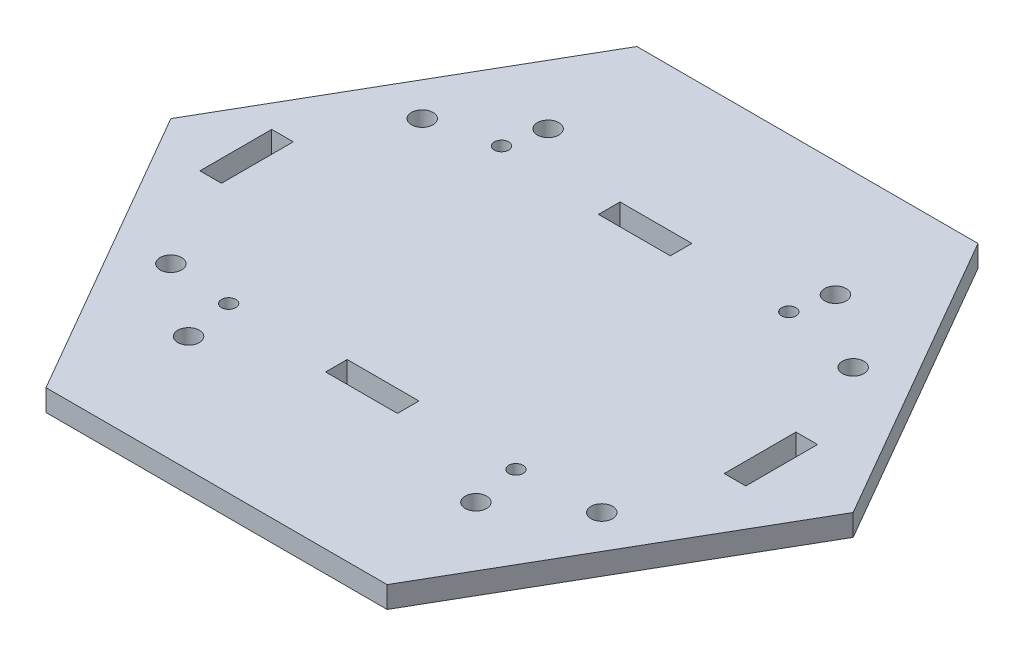
SolidWorks part; units mm, degrees
ref_plane "Alzado" through (0, 0, 0) normal (0, 0, 1) x (1, 0, 0)
ref_plane "Planta" through (0, 0, 0) normal (0, 1, 0) x (1, 0, 0)
ref_plane "Vista lateral" through (0, 0, 0) normal (1, 0, 0) x (0, 0, -1)
sketch "Croquis1" plane through (0, 0, 0) normal (0, 1, 0) x (1, 0, 0)
  line L1 (-47.5, 0) -> (-23.75, -41.1362)
  line L2 (-23.75, -41.1362) -> (23.75, -41.1362)
  line L3 (23.75, -41.1362) -> (47.5, 0)
  line L4 (47.5, 0) -> (23.75, 41.1362)
  line L5 (23.75, 41.1362) -> (-23.75, 41.1362)
  line L6 (-23.75, 41.1362) -> (-47.5, 0)
  circle A0 centre (0, 0) radius 41.1362 construction
  dimension "D1" = 95
extrude "Saliente-Extruir1" add sketch "Croquis1" along normal blind 3
sketch "Croquis3" plane through (0, 3, 0) normal (0, 1, 0) x (1, 0, 0)
  line L0 (-6.1776, 18.2235) -> (-6.1776, 21.2235)
  line L1 (33.8224, 5.7235) -> (33.8224, -4.2765)
  line L2 (3.8224, -16.7765) -> (-6.1776, -16.7765)
  line L3 (-36.1776, 5.7235) -> (-36.1776, -4.2765)
  line L4 (-6.1776, 21.2235) -> (3.8224, 21.2235)
  line L5 (3.8224, 21.2235) -> (3.8224, 18.2235)
  line L6 (33.8224, 5.7235) -> (36.8224, 5.7235)
  line L7 (36.8224, 5.7235) -> (36.8224, -4.2765)
  line L8 (36.8224, -4.2765) -> (33.8224, -4.2765)
  line L9 (-6.1776, -16.7765) -> (-6.1776, -19.7765)
  line L10 (-6.1776, -19.7765) -> (3.8224, -19.7765)
  line L11 (3.8224, -19.7765) -> (3.8224, -16.7765)
  line L12 (-36.1776, 5.7235) -> (-39.1776, 5.7235)
  line L13 (-39.1776, 5.7235) -> (-39.1776, -4.2765)
  line L14 (-39.1776, -4.2765) -> (-36.1776, -4.2765)
  line L15 (3.8224, 18.2235) -> (-6.1776, 18.2235)
  circle A0 centre (-21.1776, 19.7235) radius 1
  circle A1 centre (18.8224, 19.7235) radius 1
  circle A2 centre (18.8224, -18.2765) radius 1
  circle A3 centre (-21.1776, -18.2765) radius 1
extrude "Cortar-Extruir1" cut sketch "Croquis3" against normal through all
sketch "Croquis4" plane through (0, 3, 0) normal (0, 1, 0) x (1, 0, 0)
  line L0 (0, 0) -> (0, -76.9534) construction
  line L1 (0, 0) -> (90.3506, 0) construction
  circle A0 centre (20.005, -25.03) radius 1.5
  circle A1 centre (20.005, 25.03) radius 1.5
  circle A2 centre (-20.005, 25.03) radius 1.5
  circle A3 centre (-20.005, -25.03) radius 1.5
  point P8 (-14.8718, -18.2765)
  dimension "D1" = 50.06
  dimension "D3" = 3
  dimension "40.01" = 40.01
  dimension "D4" = 50.06
  dimension "D5" = 40.01
extrude "Cortar-Extruir2" cut sketch "Croquis4" against normal through all
sketch "Croquis5" plane through (0, 3, 0) normal (0, 1, 0) x (1, 0, 0)
  line L0 (0, 0) -> (0, -43.3492) construction
  line L1 (0, 0) -> (57.0992, 0) construction
  circle A0 centre (30, 17.5) radius 1.5
  circle A1 centre (30, -17.5) radius 1.5
  circle A2 centre (-30, -17.5) radius 1.5
  circle A3 centre (-30, 17.5) radius 1.5
  point P11 (0, 0)
  dimension "D1" = 3
  dimension "D2" = 35
  dimension "D3" = 35
  dimension "D4" = 60
  dimension "D5" = 60
extrude "Cortar-Extruir3" cut sketch "Croquis5" against normal through all
